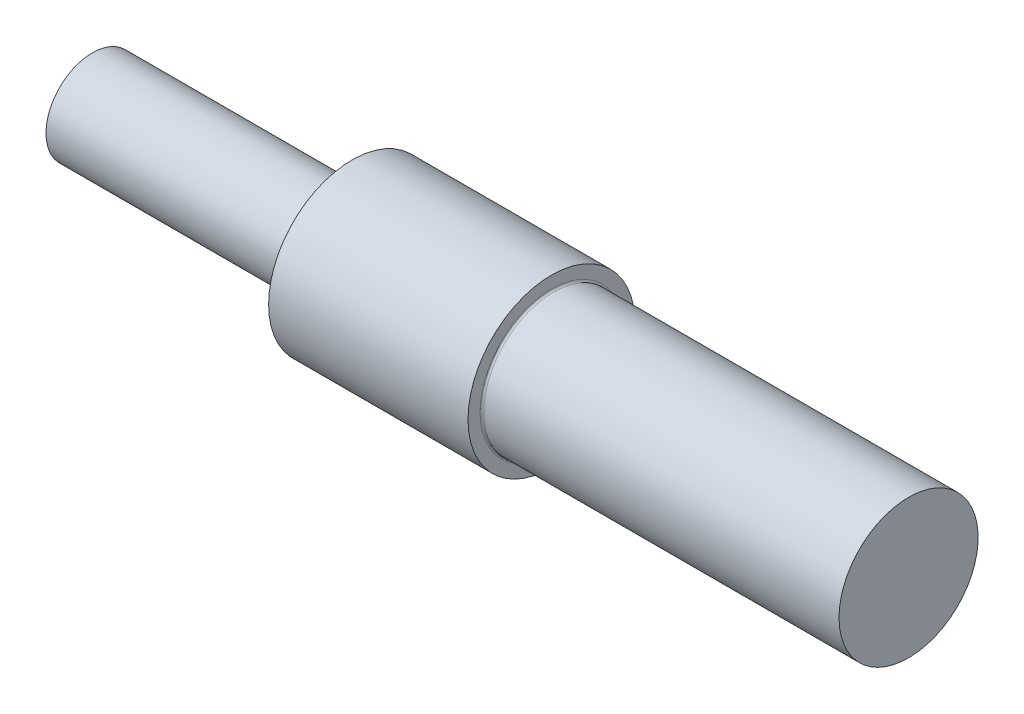
SolidWorks part; units mm, degrees
material "Stainless Steel (ferritic)"
ref_plane "Front Plane" through (0, 0, 0) normal (0, 0, 1) x (1, 0, 0)
ref_plane "Top Plane" through (0, 0, 0) normal (0, 1, 0) x (1, 0, 0)
ref_plane "Right Plane" through (0, 0, 0) normal (1, 0, 0) x (0, 0, -1)
sketch "Sketch1" plane through (0, 0, 0) normal (0, 0, 1) x (1, 0, 0)
  line L0 (-49.8127, 0) -> (102.0242, 0) construction
  line L1 (55, 0) -> (-55, 0) construction
  line L2 (-1, 5) -> (-28, 5)
  line L3 (0, -55) -> (0, 55) construction
  line L4 (-28, 5) -> (-28, 0)
  line L5 (-28, 0) -> (60, 0)
  line L6 (60, 0) -> (60, 7.5)
  line L7 (21.5, 9) -> (0, 9)
  line L8 (0, 9) -> (0, 5)
  line L9 (21.5, 9) -> (21.5, 7.7)
  line L10 (21.7, 7.5) -> (60, 7.5)
  arc A0 (21.5, 7.7) -> (21.7, 7.5) centre (21.7, 7.7) ccw
  arc A1 (-1, 5) -> (0, 5) centre (-0.5, 5) ccw
  dimension "D7" = 0.2
  dimension "D8" = 1
  dimension "D1" = 18
  dimension "D2" = 10
  dimension "D3" = 28
  dimension "D4" = 60
  dimension "D5" = 15
  dimension "D6" = 21.5
revolve "Revolve1" add sketch "Sketch1" angle 360 about L0
